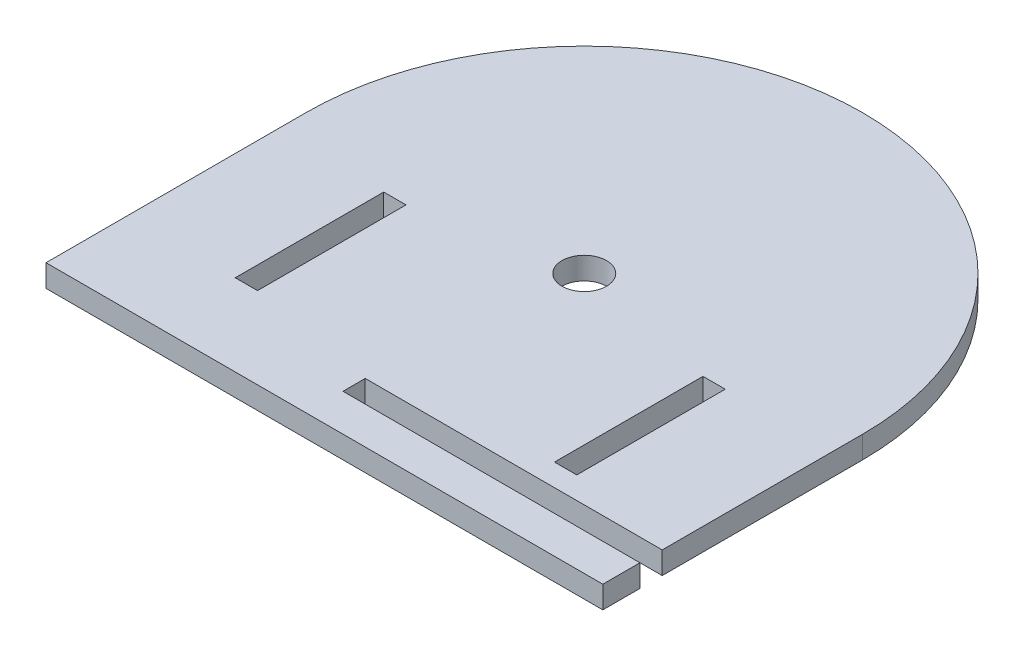
SolidWorks part; units mm, degrees
ref_plane "Front Plane" through (0, 0, 0) normal (0, 0, 1) x (1, 0, 0)
ref_plane "Top Plane" through (0, 0, 0) normal (0, 1, 0) x (1, 0, 0)
ref_plane "Right Plane" through (0, 0, 0) normal (1, 0, 0) x (0, 0, -1)
sketch "Sketch1" plane through (0, 0, 0) normal (0, 1, 0) x (1, 0, 0)
  line L15 (145, 35) -> (145, 8)
  line L17 (70, 35) -> (70, 0)
  line L18 (70, 0) -> (145, 0)
  line L20 (145, 8) -> (105, 8)
  line L22 (145, 5) -> (105, 5)
  line L23 (105, 8) -> (105, 5)
  line L24 (145, 5) -> (145, 0)
  line L32 (107.5, 20.9892) -> (87.5, 20.9892) construction
  line L41 (107.5, 72.5) -> (107.5, 0) construction
  line L42 (107.5, 20.9892) -> (127.5, 20.9892) construction
  line L53 (87.5, 20.9892) -> (87.5, 30.9892)
  line L54 (87.5, 30.9892) -> (84.5, 30.9892)
  line L55 (84.5, 30.9892) -> (84.5, 10.9892)
  line L56 (84.5, 10.9892) -> (87.5, 10.9892)
  line L57 (87.5, 10.9892) -> (87.5, 20.9892)
  line L58 (127.5, 20.9892) -> (127.5, 30.9892)
  line L59 (127.5, 30.9892) -> (130.5, 30.9892)
  line L60 (130.5, 30.9892) -> (130.5, 10.9892)
  line L61 (130.5, 10.9892) -> (127.5, 10.9892)
  line L62 (127.5, 10.9892) -> (127.5, 20.9892)
  line L64 (84.5, 30.9892) -> (87.5, 30.9892)
  line L65 (84.5, 30.9892) -> (84.5, 10.9892)
  line L66 (84.5, 10.9892) -> (87.5, 10.9892)
  line L67 (87.5, 30.9892) -> (87.5, 10.9892)
  line L68 (127.5, 30.9892) -> (130.5, 30.9892)
  line L69 (127.5, 30.9892) -> (127.5, 10.9892)
  line L70 (127.5, 10.9892) -> (130.5, 10.9892)
  line L71 (130.5, 30.9892) -> (130.5, 10.9892)
  arc A1 (70, 35) -> (145, 35) centre (107.5, 35) cw
  circle A2 centre (107.5, 35) radius 3
extrude "Boss-Extrude6" add sketch "Sketch1" along normal blind 3 contours A1 L17 L18 L24 L22 L23 L20 L15 A2 L57 L56 L55 L54 L53 L61 L62 L58 L59 L60
